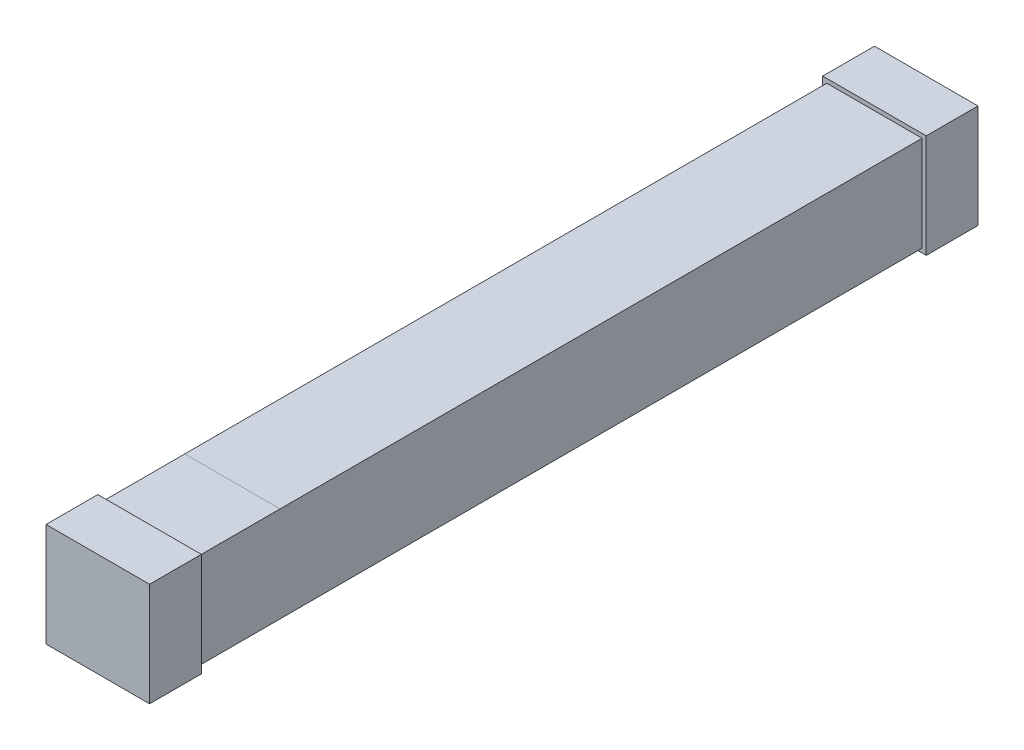
SolidWorks part; units mm, degrees
ref_plane "Front Plane" through (0, 0, 0) normal (0, 0, 1) x (1, 0, 0)
ref_plane "Top Plane" through (0, 0, 0) normal (0, 1, 0) x (1, 0, 0)
ref_plane "Right Plane" through (0, 0, 0) normal (1, 0, 0) x (0, 0, -1)
sketch "Sketch1" plane through (0, 0, 0) normal (0, 0, 1) x (1, 0, 0)
  line L0 (0.46, 0.04) -> (-0.46, 0.96) construction
  line L1 (-0.46, 0.96) -> (0.46, 0.96)
  line L2 (-0.46, 0.96) -> (-0.46, 0.04)
  line L3 (-0.46, 0.04) -> (0.46, 0.04)
  line L4 (0.46, 0.96) -> (0.46, 0.04)
  line L5 (0, 0) -> (0, 0.5) construction
  dimension "D1" = 0.04
  dimension "D2" = 0.92
extrude "Boss-Extrude1" add sketch "Sketch1" along normal mid plane 7
sketch "Sketch2" plane through (0, 0, 3.5) normal (0, 0, 1) x (1, 0, 0)
  line L14 (0.5, 0) -> (0.5, 1)
  line L15 (-0.5, 0) -> (0.5, 0)
  line L16 (-0.5, 1) -> (-0.5, 0)
  line L17 (0.5, 1) -> (-0.5, 1)
  line L18 (0.5, 0) -> (0.5, 1)
  line L19 (-0.5, 0) -> (0.5, 0)
  line L20 (-0.5, 1) -> (-0.5, 0)
  line L21 (0.5, 1) -> (-0.5, 1)
  dimension "D1" = 0.04
extrude "Boss-Extrude2" add sketch "Sketch2" along normal blind 0.5
mirror "Mirror1" about plane through (0, 0, 0) normal (0, 0, 1) of "Boss-Extrude2"
sketch "Sketch4" plane through (0, 0.96, 0) normal (0, 1, 0) x (1, 0, 0)
  line L0 (0.46, -3.5) -> (0.46, 3.5) construction
  line L1 (-0.46, -3.5) -> (0.46, -3.5)
  line L2 (-0.46, -3.5) -> (-0.46, -2.7)
  line L3 (-0.46, -2.7) -> (0.46, -2.7)
  line L4 (0.46, -3.5) -> (0.46, -2.7)
  dimension "D1" = 0.8
split line "Split Line1"
